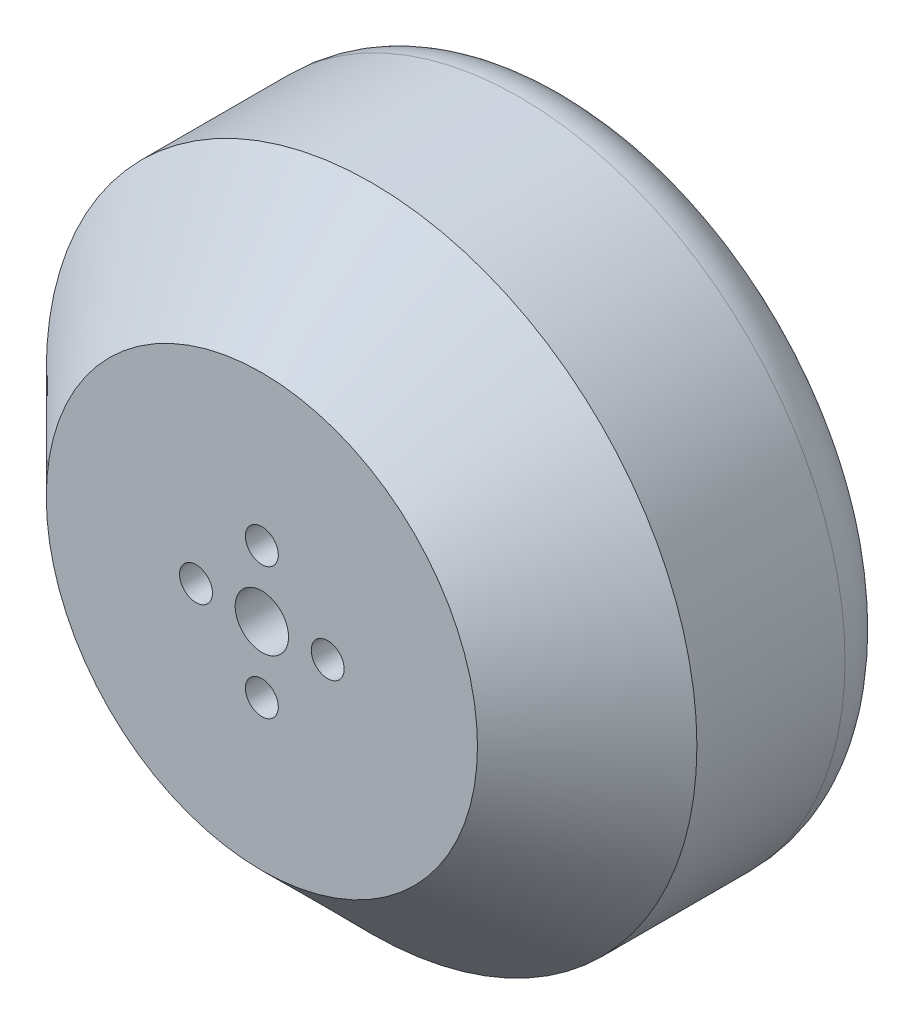
SolidWorks part; units mm, degrees
ref_plane "前视基准面" through (0, 0, 0) normal (0, 0, 1) x (1, 0, 0)
ref_plane "上视基准面" through (0, 0, 0) normal (0, 1, 0) x (1, 0, 0)
ref_plane "右视基准面" through (0, 0, 0) normal (1, 0, 0) x (0, 0, -1)
sketch "Sketch1" plane through (0, 0, 0) normal (0, 0, 1) x (1, 0, 0)
  circle A0 centre (-37.2475, 0) radius 29.65
  dimension "D1" = 59.3
extrude "Boss-Extrude1" add sketch "Sketch1" along normal blind 28.5
chamfer "Chamfer1" distance 10 angle 45 1 edges at (-7.5975, 0, 28.5)
fillet "Fillet1" radius 5 1 edges at (-7.5975, 0, 0)
sketch "Sketch2" plane through (0, 0, 28.5) normal (0, 0, 1) x (1, 0, 0)
  circle A0 centre (-37.2475, 0) radius 6 construction
  circle A1 centre (-37.2475, 6) radius 1.5
  circle A2 centre (-43.2475, 0) radius 1.5
  circle A3 centre (-37.2475, -6) radius 1.5
  circle A4 centre (-31.2475, 0) radius 1.5
  circle A5 centre (-37.2475, 0) radius 2.4297
  dimension "D1" = 12
extrude "Cut-Extrude1" cut sketch "Sketch2" against normal blind 9.5
sketch "Sketch3" plane through (0, 0, 0) normal (0, 0, -1) x (-1, 0, 0)
  circle A0 centre (37.2475, 0) radius 12.5 construction
  circle A1 centre (37.2475, 12.5) radius 1.5
  circle A2 centre (49.7475, 0) radius 1.5
  circle A3 centre (24.7614, 0.589) radius 1.5
  circle A4 centre (37.2475, -12.5) radius 1.5
extrude "Cut-Extrude2" cut sketch "Sketch3" against normal blind 9.5
